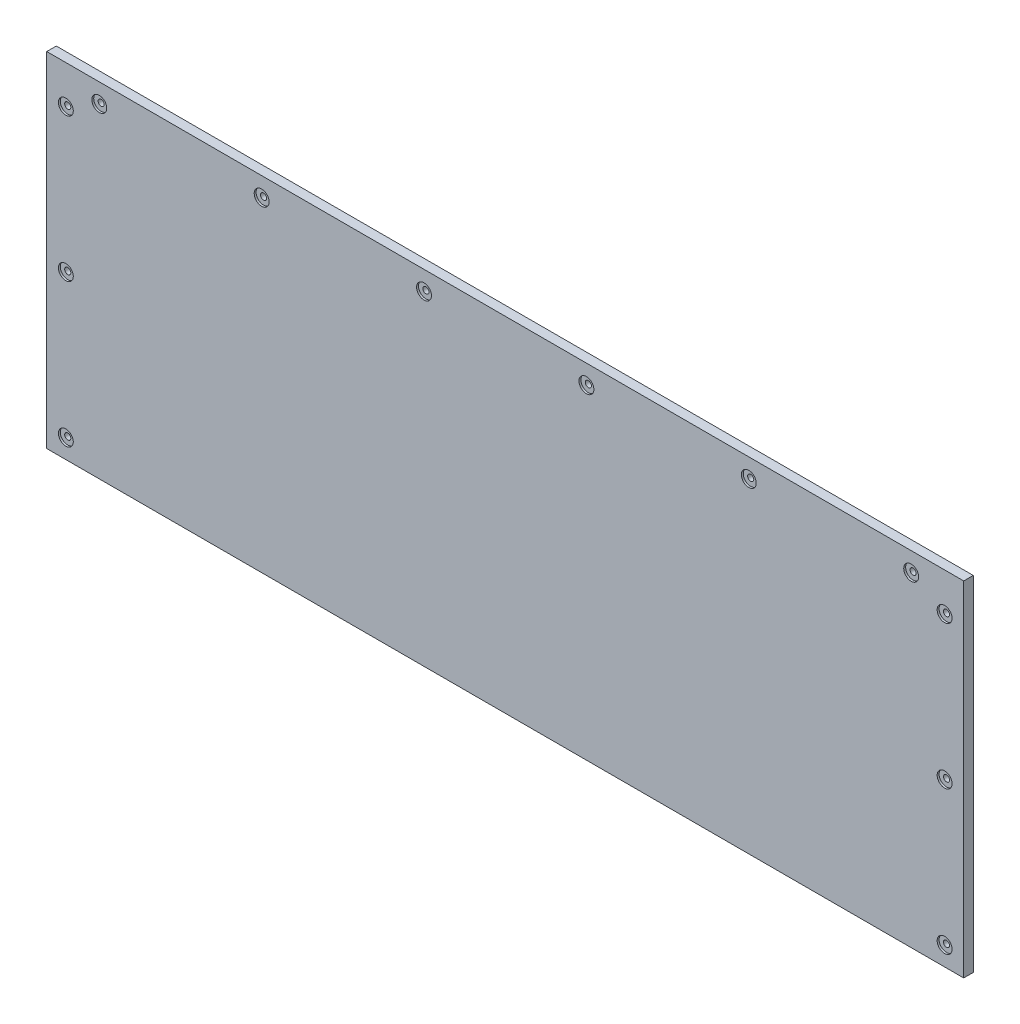
SolidWorks part; units mm, degrees
ref_plane "Front Plane" through (0, 0, 0) normal (0, 0, 1) x (1, 0, 0)
ref_plane "Top Plane" through (0, 0, 0) normal (0, 1, 0) x (1, 0, 0)
ref_plane "Right Plane" through (0, 0, 0) normal (1, 0, 0) x (0, 0, -1)
sketch "Sketch1" plane through (0, 0, 0) normal (0, 0, 1) x (1, 0, 0)
  line L1 (0, 0) -> (609.6, 0)
  line L2 (0, 0) -> (0, 228.6)
  line L3 (0, 228.6) -> (609.6, 228.6)
  line L4 (609.6, 0) -> (609.6, 228.6)
  dimension "D1" = 228.6
  dimension "D2" = 609.6
extrude "Boss-Extrude1" add sketch "Sketch1" along normal blind 6.35 contours L2 L3 L4 L1
sketch "Sketch2" plane through (0, 0, 6.35) normal (0, 0, 1) x (1, 0, 0)
  line L0 (0, 0) -> (0, 228.6) construction
  line L1 (0, 228.6) -> (609.6, 228.6) construction
  line L2 (304.8, 228.6) -> (304.8, 0) construction
  line L3 (0, 0) -> (609.6, 0) construction
  circle A0 centre (12.7, 203.2) radius 2.032
  circle A3 centre (12.7, 107.95) radius 2.032
  circle A4 centre (12.7, 12.7) radius 2.032
  circle A5 centre (596.9, 12.7) radius 2.032
  circle A6 centre (596.9, 107.95) radius 2.032
  circle A7 centre (596.9, 203.2) radius 2.032
  dimension "D3" = 4.064
  dimension "D4" = 3
  dimension "D1" = 12.7
  dimension "D2" = 25.4
extrude "Cut-Extrude4" cut sketch "Sketch2" against normal through all contours A0 | A3 | A4 | A5 | A6 | A7
sketch "Sketch3" plane through (0, 0, 6.35) normal (0, 0, 1) x (1, 0, 0)
  line L0 (304.8, 228.6) -> (304.8, 0) construction
  line L1 (0, 228.6) -> (609.6, 228.6) construction
  line L2 (0, 0) -> (609.6, 0) construction
  circle A0 centre (12.7, 203.2) radius 4.953
  circle A1 centre (12.7, 107.95) radius 4.953
  circle A2 centre (12.7, 12.7) radius 4.953
  circle A3 centre (596.9, 12.7) radius 4.953
  circle A4 centre (596.9, 107.95) radius 4.953
  circle A5 centre (596.9, 203.2) radius 4.953
  dimension "D1" = 9.906
  dimension "D2" = 3
extrude "Cut-Extrude6" cut sketch "Sketch3" against normal blind 1.27
sketch "Sketch4" plane through (0, 0, 6.35) normal (0, 0, 1) x (1, 0, 0)
  line L0 (0, 228.6) -> (609.6, 228.6) construction
  line L1 (0, 0) -> (0, 228.6) construction
  circle A0 centre (34.925, 215.9) radius 2.032
  circle A1 centre (142.875, 215.9) radius 2.032
  circle A2 centre (250.825, 215.9) radius 2.032
  circle A3 centre (358.775, 215.9) radius 2.032
  circle A4 centre (466.725, 215.9) radius 2.032
  circle A5 centre (574.675, 215.9) radius 2.032
  dimension "D1" = 4.064
  dimension "D2" = 12.7
  dimension "D3" = 34.925
  dimension "D4" = 107.95
extrude "Cut-Extrude7" cut sketch "Sketch4" against normal through all
sketch "Sketch5" plane through (0, 0, 6.35) normal (0, 0, 1) x (1, 0, 0)
  circle A0 centre (34.925, 215.9) radius 4.953
  circle A1 centre (142.875, 215.9) radius 4.953
  circle A2 centre (250.825, 215.9) radius 4.953
  circle A3 centre (358.775, 215.9) radius 4.953
  circle A4 centre (466.725, 215.9) radius 4.953
  circle A5 centre (574.675, 215.9) radius 4.953
  dimension "D1" = 9.906
extrude "Cut-Extrude8" cut sketch "Sketch5" against normal blind 1.27
